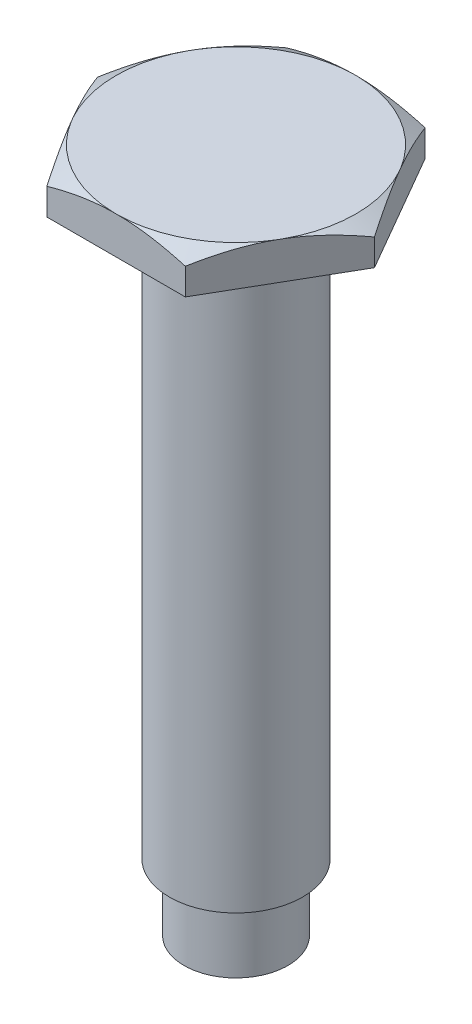
SolidWorks part; units mm, degrees
material "Plain Carbon Steel"
ref_plane "Front Plane" through (0, 0, 0) normal (0, 0, 1) x (1, 0, 0)
ref_plane "Top Plane" through (0, 0, 0) normal (0, 1, 0) x (1, 0, 0)
ref_plane "Right Plane" through (0, 0, 0) normal (1, 0, 0) x (0, 0, -1)
sketch "Sketch1" plane through (0, 0, 0) normal (0, 1, 0) x (1, 0, 0)
  line L1 (5.195, 0) -> (2.5975, 4.499)
  line L2 (2.5975, 4.499) -> (-2.5975, 4.499)
  line L3 (-2.5975, 4.499) -> (-5.195, 0)
  line L4 (-5.195, 0) -> (-2.5975, -4.499)
  line L5 (-2.5975, -4.499) -> (2.5975, -4.499)
  line L6 (2.5975, -4.499) -> (5.195, 0)
  circle A0 centre (0, 0) radius 4.499 construction
  dimension "D2" = 8.998
  dimension "D1" = 5.195
extrude "Boss-Extrude1" add sketch "Sketch1" along normal blind 1.4
sketch "Sketch2" plane through (0, 1.4, 0) normal (0, 1, 0) x (1, 0, 0)
  circle A0 centre (0, 0) radius 4.5
  dimension "D1" = 9
extrude "Cut-Extrude1" cut sketch "Sketch2" against normal blind 1 draft 60 flip side to cut contours A0
sketch "Sketch3" plane through (0, 0, 0) normal (0, -1, 0) x (1, 0, 0)
  circle A0 centre (0, 0) radius 2.5
  dimension "D1" = 5
extrude "Boss-Extrude2" add sketch "Sketch3" along normal blind 24.3
cosmetic thread "Cosmetic Thread1" parameters "D1"=10.3, "D2"=4.11
sketch "Sketch4" plane through (0, -24.3, 0) normal (0, -1, 0) x (1, 0, 0)
  circle A0 centre (0, 0) radius 1.95
  dimension "D1" = 3.9
extrude "Cut-Extrude2" cut sketch "Sketch4" against normal blind 2.5 flip side to cut
